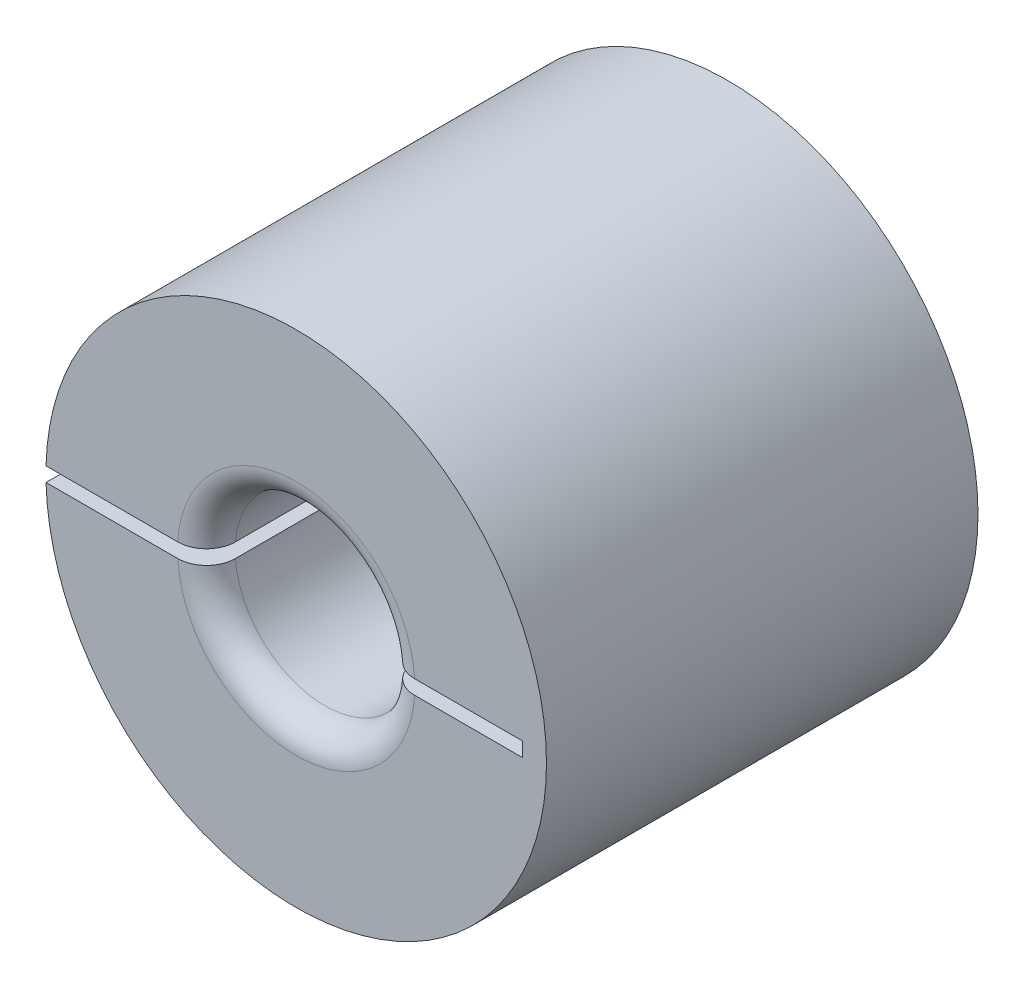
SolidWorks part; units mm, degrees
material "Copper"
ref_plane "Front Plane" through (0, 0, 0) normal (0, 0, 1) x (1, 0, 0)
ref_plane "Top Plane" through (0, 0, 0) normal (0, 1, 0) x (1, 0, 0)
ref_plane "Right Plane" through (0, 0, 0) normal (1, 0, 0) x (0, 0, -1)
sketch "Sketch1" plane through (0, 0, 0) normal (0, 0, 1) x (1, 0, 0)
  circle A0 centre (0, 0) radius 11.049
  circle A1 centre (0, 0) radius 3.9688
extrude "Boss-Extrude1" add sketch "Sketch1" along normal blind 19.05
fillet "Fillet1" radius 1.27 2 edges at (3.9688, 0, 0) (3.9688, 0, 19.05)
sketch "Sketch3" plane through (0, 0, 19.05) normal (0, 0, 1) x (1, 0, 0)
  line L0 (11.049, 0) -> (-19.812, 0)
  line L2 (-11.549, -0.3175) -> (9.9809, -0.3175)
  line L3 (-11.549, -0.3175) -> (-11.549, 0.3175)
  line L4 (-11.549, 0.3175) -> (9.9809, 0.3175)
  line L5 (9.9809, -0.3175) -> (9.9809, 0.3175)
  circle A0 centre (0, 0) radius 11.049 construction
  dimension "D1" = 0.635
  dimension "D2" = 0.3175
extrude "Cut-Extrude1" cut sketch "Sketch3" against normal through all contours L4 L5 L2 L3
